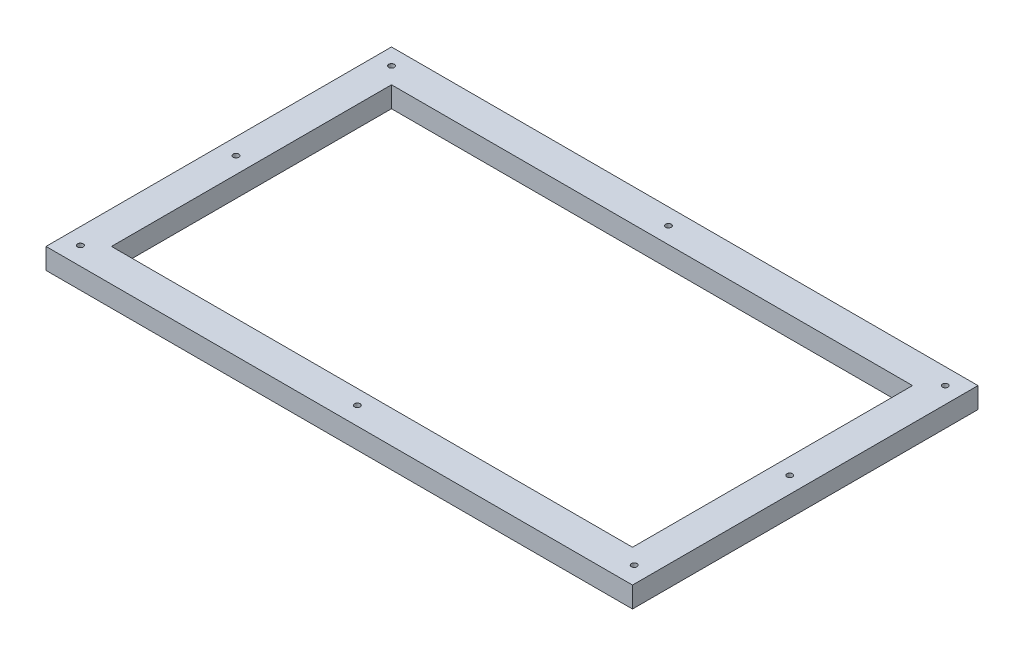
SolidWorks part; units mm, degrees
ref_plane "Front Plane" through (0, 0, 0) normal (0, 0, 1) x (1, 0, 0)
ref_plane "Top Plane" through (0, 0, 0) normal (0, 1, 0) x (1, 0, 0)
ref_plane "Right Plane" through (0, 0, 0) normal (1, 0, 0) x (0, 0, -1)
sketch "Sketch1" plane through (0, 0, 0) normal (0, 1, 0) x (1, 0, 0)
  line L1 (-179.135, 105.525) -> (179.135, 105.525)
  line L2 (-179.135, 105.525) -> (-179.135, -105.525)
  line L3 (-179.135, -105.525) -> (179.135, -105.525)
  line L4 (179.135, 105.525) -> (179.135, -105.525)
  line L5 (-179.135, 105.525) -> (179.135, -105.525) construction
  line L6 (-179.135, -105.525) -> (179.135, 105.525) construction
  point P0 (0, 0)
  dimension "D1" = 358.27
  dimension "D2" = 211.05
extrude "Boss-Extrude1" add sketch "Sketch1" along normal blind 12.7
sketch "Sketch2" plane through (0, 12.7, 0) normal (0, 1, 0) x (1, 0, 0)
  line L0 (179.135, 105.525) -> (-179.135, 105.525) construction
  line L1 (-159.135, 85.525) -> (159.135, 85.525)
  line L2 (-159.135, 85.525) -> (-159.135, -85.525)
  line L3 (-159.135, -85.525) -> (159.135, -85.525)
  line L4 (159.135, 85.525) -> (159.135, -85.525)
  line L5 (-159.135, 85.525) -> (159.135, -85.525) construction
  line L6 (-159.135, -85.525) -> (159.135, 85.525) construction
  line L7 (-179.135, 105.525) -> (-179.135, -105.525) construction
  point P0 (0, 0)
  dimension "D1" = 20
  dimension "D2" = 20
extrude "Cut-Extrude1" cut sketch "Sketch2" against normal blind 12.7
hole_wizard "M3 Clearance Hole1" positions "Sketch3" profile "Sketch4" hole size "M3" standard "ANSI Metric"
sketch "Sketch3" plane through (0, 12.7, 0) normal (0, 1, 0) x (1, 0, 0)
  point P0 (-169.135, 95.525)
  point P3 (-169.135, 0.525)
  point P6 (-169.135, -94.475)
  point P9 (0, -94.475)
  point P12 (169.135, -94.475)
  point P15 (167.8251, 1.3591)
  point P19 (169.135, 0.525)
  point P22 (167.6465, 95.3588)
  point P24 (169.135, 95.525)
  point P28 (0, 95.525)
sketch "Sketch4" plane through (-169.135, 12.7, -95.525) normal (1, 0, 0) x (0, 0, 1)
  line L0 (0, 0) -> (0, 12.7)
  line L1 (0, 12.7) -> (1.7, 12.7)
  line L2 (1.7, 12.7) -> (1.7, 0.025)
  line L3 (1.7, 0.025) -> (1.725, 0)
  line L5 (1.725, 0) -> (0, 0)
  line L6 (-1.7, 0.025) -> (-1.725, 0) construction
  line L11 (0, -6.35) -> (0, 107.95) construction
  dimension "Thru Hole Dia." = 3.4
  dimension "Thru Hole Depth" = 12.7
  dimension "Near C'Sink Dia." = 3.45
  dimension "Near C'Sink Angle" = 90
